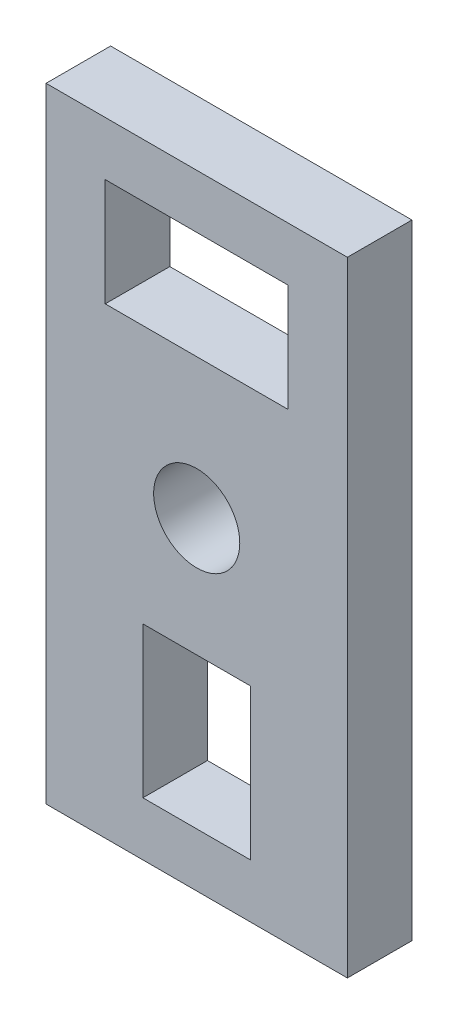
SolidWorks part; units mm, degrees
ref_plane "Plan de face" through (0, 0, 0) normal (0, 0, 1) x (1, 0, 0)
ref_plane "Plan de dessus" through (0, 0, 0) normal (0, 1, 0) x (1, 0, 0)
ref_plane "Plan de droite" through (0, 0, 0) normal (1, 0, 0) x (0, 0, -1)
sketch "Esquisse1" plane through (0, 0, 0) normal (0, 0, 1) x (1, 0, 0)
  line L1 (0, 0) -> (20, 0)
  line L2 (0, 0) -> (0, 40)
  line L3 (0, 40) -> (20, 40)
  line L4 (20, 0) -> (20, 40)
  dimension "D1" = 20
  dimension "D2" = 40
extrude "Boss.-Extru.1" add sketch "Esquisse1" along normal blind 3
sketch "Esquisse2" plane through (0, 0, 3) normal (0, 0, 1) x (1, 0, 0)
  line L0 (20, 0) -> (20, 40) construction
  line L1 (5.75, 31.5) -> (14.25, 31.5)
  line L2 (5.75, 31.5) -> (5.75, 26.5)
  line L3 (5.75, 26.5) -> (14.25, 26.5)
  line L4 (14.25, 31.5) -> (14.25, 26.5)
  line L5 (7.5, 14.5) -> (12.5, 14.5)
  line L6 (7.5, 14.5) -> (7.5, 7.5)
  line L7 (7.5, 7.5) -> (12.5, 7.5)
  line L8 (12.5, 14.5) -> (12.5, 7.5)
  line L9 (0, 0) -> (20, 0) construction
  line L10 (20, 40) -> (0, 40) construction
  circle A0 centre (10, 20) radius 2
  dimension "D1" = 8.5
  dimension "D9" = 10
  dimension "D10" = 20
  dimension "D2" = 5
  dimension "D3" = 5
  dimension "D4" = 7
  dimension "D5" = 7.5
  dimension "D6" = 7.5
  dimension "D7" = 5.75
  dimension "D8" = 8.5
extrude "Enlèv. mat.-Extru.1" cut sketch "Esquisse2" against normal up to next
sketch "Esquisse3" plane through (0, 0, 3) normal (0, 0, 1) x (1, 0, 0)
  line L0 (20, 40) -> (0, 40) construction
  line L1 (0, 0) -> (3, 0)
  line L2 (0, 0) -> (0, 40)
  line L3 (0, 40) -> (3, 40)
  line L4 (3, 0) -> (3, 40)
  line L6 (17, 40) -> (20, 40)
  line L7 (17, 40) -> (17, 0)
  line L8 (17, 0) -> (20, 0)
  line L9 (20, 40) -> (20, 0)
  line L10 (3, 40) -> (17, 40)
  line L12 (3, 34) -> (17, 34)
  line L14 (3, 0) -> (17, 0)
  line L16 (3, 5) -> (17, 5)
  line M18 (0, 40) -> (0, 0)
  line M19 (0, 0) -> (20, 0)
  line M20 (20, 0) -> (20, 40)
  line M21 (20, 40) -> (0, 40)
  dimension "D1" = 3
  dimension "D2" = 3
  dimension "D3" = 6
  dimension "D4" = 5
extrude "Enlèv. mat.-Extru.2" cut sketch "Esquisse3" against normal up to next contours L4 M19 M21 M18 | L7 M21 M19 M20 | L16 L4 L7 M19 | L4 L12 L7 M21
